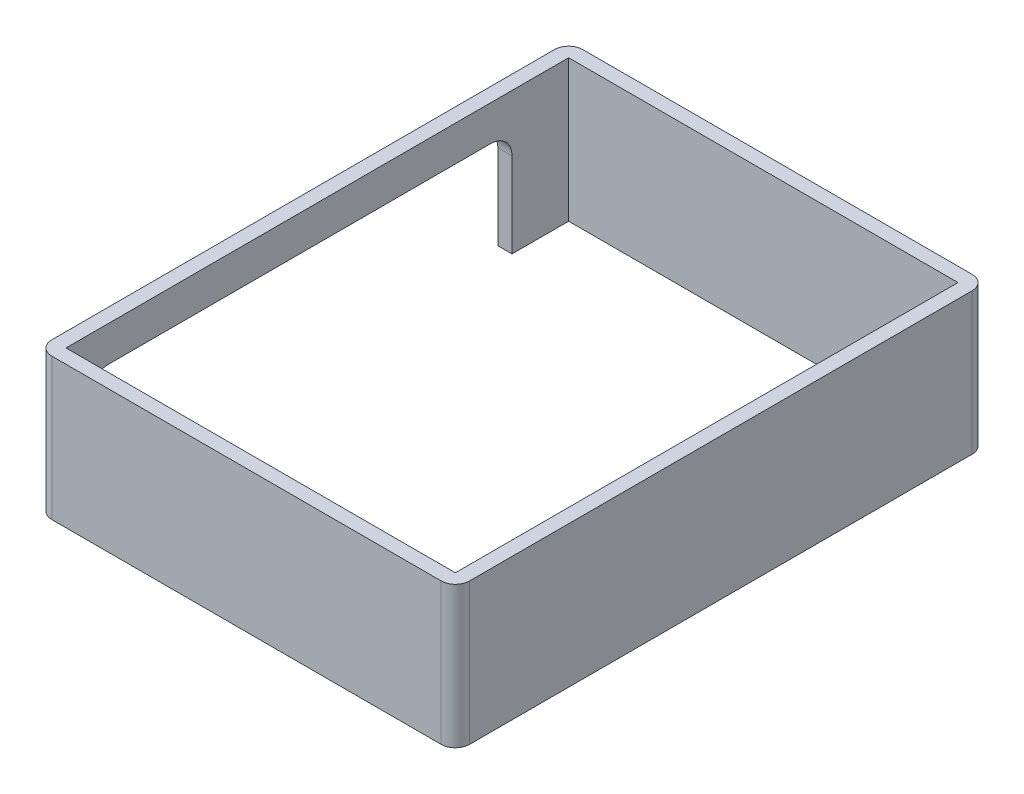
SolidWorks part; units mm, degrees
ref_plane "Front Plane" through (0, 0, 0) normal (0, 0, 1) x (1, 0, 0)
ref_plane "Top Plane" through (0, 0, 0) normal (0, 1, 0) x (1, 0, 0)
ref_plane "Right Plane" through (0, 0, 0) normal (1, 0, 0) x (0, 0, -1)
sketch "Sketch1" plane through (0, 0, 0) normal (0, 1, 0) x (1, 0, 0)
  line L0 (29.5, -35.5) -> (29.5, 35.5)
  line L1 (27.5, 37.5) -> (-27.5, 37.5)
  line L2 (-29.5, 35.5) -> (-29.5, -35.5)
  line L3 (-27.5, -37.5) -> (27.5, -37.5)
  line L4 (0, 0) -> (137.7222, 0) construction
  line L5 (0, 0) -> (0, 102.435) construction
  line L6 (27.5, -35.5) -> (27.5, 35.5)
  line L7 (27.5, 35.5) -> (-27.5, 35.5)
  line L8 (-27.5, 35.5) -> (-27.5, -35.5)
  line L9 (-27.5, -35.5) -> (27.5, -35.5)
  arc A0 (27.5, -37.5) -> (29.5, -35.5) centre (27.5, -35.5) ccw
  arc A1 (29.5, 35.5) -> (27.5, 37.5) centre (27.5, 35.5) ccw
  arc A2 (-27.5, 37.5) -> (-29.5, 35.5) centre (-27.5, 35.5) ccw
  arc A3 (-29.5, -35.5) -> (-27.5, -37.5) centre (-27.5, -35.5) ccw
  arc A4 (27.5, 35.5) -> (27.5, 35.5) centre (27.5, 35.5) ccw
  arc A5 (-27.5, 35.5) -> (-27.5, 35.5) centre (-27.5, 35.5) ccw
  arc A6 (-27.5, -35.5) -> (-27.5, -35.5) centre (-27.5, -35.5) ccw
  arc A7 (27.5, -35.5) -> (27.5, -35.5) centre (27.5, -35.5) ccw
  dimension "D3" = 2
  dimension "D4" = 2
  dimension "D5" = 2
  dimension "D6" = 2
  dimension "D1" = 75
  dimension "D2" = 59
  dimension "D7" = 2
extrude "Boss-Extrude1" add sketch "Sketch1" along normal blind 20
sketch "Sketch2" plane through (-29.5, 0, 0) normal (-1, 0, 0) x (0, 0, 1)
  line L0 (-35.5, 20) -> (35.5, 20) construction
  line L1 (-24.5, 15) -> (29.5, 15)
  line L2 (-27.5, 12) -> (-27.5, -3)
  line L3 (-27.5, -3) -> (32.5, -3)
  line L4 (32.5, 12) -> (32.5, -3)
  line L5 (-27.5, 15) -> (32.5, -3) construction
  line L6 (-27.5, -3) -> (32.5, 15) construction
  line L7 (-37.5, 20) -> (-37.5, 0) construction
  arc A0 (29.5, 15) -> (32.5, 12) centre (29.5, 12) cw
  arc A1 (-24.5, 15) -> (-27.5, 12) centre (-24.5, 12) ccw
  point P0 (2.5, 6)
  dimension "D5" = 3
  dimension "D1" = 60
  dimension "D2" = 18
  dimension "D3" = 5
  dimension "D4" = 10
extrude "Cut-Extrude1" cut sketch "Sketch2" against normal blind 20
